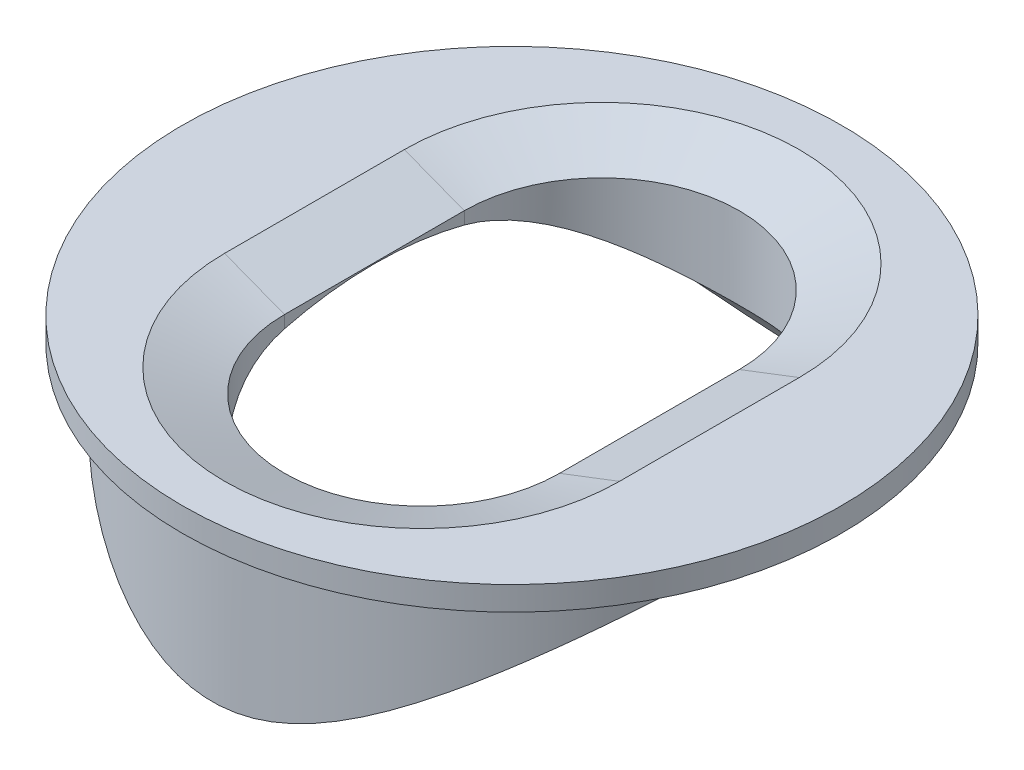
SolidWorks part; units mm, degrees
ref_plane "Front Plane" through (0, 0, 0) normal (0, 0, 1) x (1, 0, 0)
ref_plane "Top Plane" through (0, 0, 0) normal (0, 1, 0) x (1, 0, 0)
ref_plane "Right Plane" through (0, 0, 0) normal (1, 0, 0) x (0, 0, -1)
sketch "Sketch1" plane through (0, 0, 0) normal (0, 1, 0) x (1, 0, 0)
  circle A0 centre (0, 0) radius 5
extrude "Boss-Extrude1" add sketch "Sketch1" along normal blind 5
sketch "Sketch2" plane through (0, 5, 0) normal (0, 1, 0) x (1, 0, 0)
  circle A0 centre (0, 0) radius 5.5
extrude "Boss-Extrude2" add sketch "Sketch2" along normal blind 0.4
sketch "Sketch4" plane through (0, 5.4, 0) normal (0, 1, 0) x (1, 0, 0)
  line L0 (0, 1.5) -> (0, -1.5) construction
  line L1 (2.2953, 1.5) -> (2.2953, -1.5)
  line L2 (-2.2953, 1.5) -> (-2.2953, -1.5)
  arc A0 (2.2953, 1.5) -> (-2.2953, 1.5) centre (0, 1.5) ccw
  arc A1 (-2.2953, -1.5) -> (2.2953, -1.5) centre (0, -1.5) ccw
  point P3 (0, 0)
  dimension "D1" = 1.5
  dimension "D2" = 1.5
extrude "Cut-Extrude1" cut sketch "Sketch4" against normal through all
sketch "Sketch5" plane through (0, 0, 0) normal (1, 0, 0) x (0, 0, -1)
  circle A0 centre (0, -1) radius 6
extrude "Cut-Extrude2" cut sketch "Sketch5" against normal through all and the other way through all
sketch "Sketch6" plane through (0, 5.4, 0) normal (0, 1, 0) x (-1, 0, 0)
  circle A0 centre (0, 0) radius 5
chamfer "Chamfer4" distance 1 angle 21 4 edges at (0, 5.4, -3.7953) (-2.2953, 5.4, 0) (2.2953, 5.4, 0) (0, 5.4, 3.7953)
